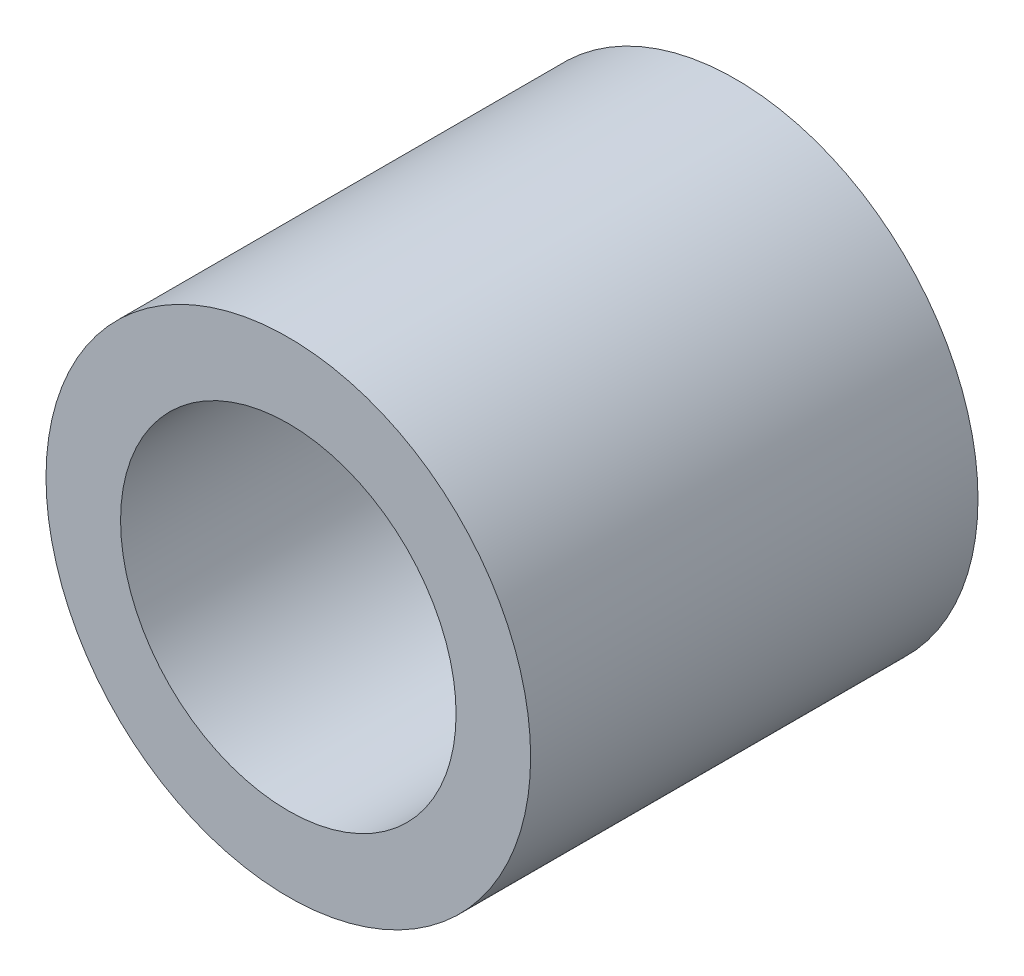
SolidWorks part; units mm, degrees
ref_plane "Front Plane" through (0, 0, 0) normal (0, 0, 1) x (1, 0, 0)
ref_plane "Top Plane" through (0, 0, 0) normal (0, 1, 0) x (1, 0, 0)
ref_plane "Right Plane" through (0, 0, 0) normal (1, 0, 0) x (0, 0, -1)
sketch "Sketch1" plane through (0, 0, 0) normal (0, 0, 1) x (1, 0, 0)
  circle A0 centre (0, 0) radius 2.25
  circle A1 centre (0, 0) radius 3.25
  dimension "D1" = 4.5
  dimension "D2" = 6.5
extrude "Boss-Extrude1" add sketch "Sketch1" along normal blind 6
